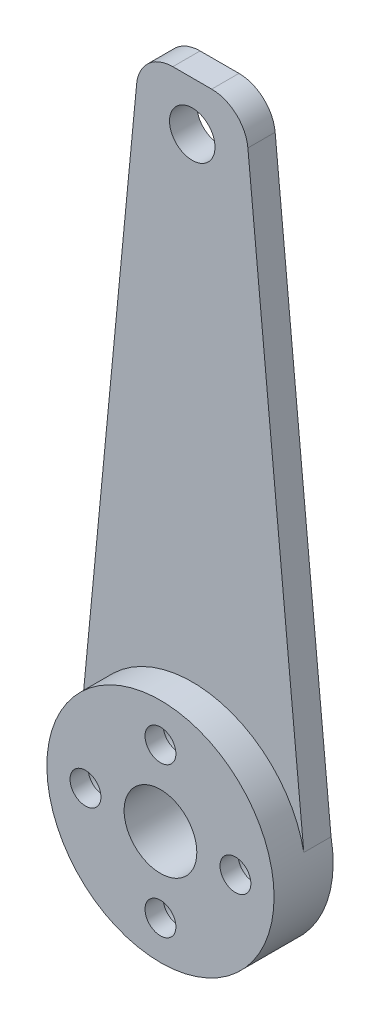
SolidWorks part; units mm, degrees
ref_plane "Plan de face" through (0, 0, 0) normal (0, 0, 1) x (1, 0, 0)
ref_plane "Plan de dessus" through (0, 0, 0) normal (0, 1, 0) x (1, 0, 0)
ref_plane "Plan de droite" through (0, 0, 0) normal (1, 0, 0) x (0, 0, -1)
sketch "Esquisse2" plane through (0, 0, 0) normal (0, 0, 1) x (1, 0, 0)
  circle A0 centre (0, 0) radius 12.5
  circle A1 centre (0, 0) radius 8.25
  dimension "D1" = 25
  dimension "D2" = 16.5
extrude "Boss.-Extru.1" add sketch "Esquisse2" along normal mid plane 6.5 contours A0
sketch "Esquisse3" plane through (0, 0, 0) normal (0, 0, 1) x (1, 0, 0)
  circle A2 centre (0, 8.25) radius 1.2
  circle A3 centre (-8.25, 0) radius 1.2
  circle A4 centre (0, -8.25) radius 1.2
  circle A5 centre (8.25, 0) radius 1.2
  point P3 (-8.25, 0)
  point P11 (0, 8.25)
  point P12 (8.25, 0)
  point P13 (0, -8.25)
  dimension "D1" = 2.4
  dimension "D2" = 2.4
  dimension "D3" = 2.4
  dimension "D4" = 2.4
extrude "Enlèv. mat.-Extru.1" cut sketch "Esquisse3" along normal through all
sketch "Esquisse20" plane through (0, 0, -3.25) normal (0, 0, -1) x (-1, 0, 0)
  line L0 (-12.5, 0) -> (-5.7722, 70.0532)
  line L1 (-5.7722, 70.0532) -> (5.7722, 70.0532)
  line L2 (5.7722, 70.0532) -> (12.5, 0)
  line L3 (12.5, 0) -> (-12.5, 0)
  circle A0 centre (0, 0) radius 12.5 construction
  point P4 (0, 70.0532)
extrude "Boss.-Extru.2" add sketch "Esquisse20" against normal blind 3
sketch "Esquisse10" plane through (0, 0, -3.25) normal (0, 0, -1) x (-1, 0, 0)
  circle A0 centre (-8.25, 0) radius 1.7
  circle A1 centre (0, 8.25) radius 1.7
  circle A2 centre (8.25, 0) radius 1.7
  circle A3 centre (0, -8.25) radius 1.7
  dimension "D1" = 3.4
  dimension "D2" = 3.4
  dimension "D3" = 3.4
  dimension "D4" = 3.4
extrude "Enlèv. mat.-Extru.2" cut sketch "Esquisse10" against normal through all and the other way through all
sketch "Esquisse11" plane through (0, 0, -3.25) normal (0, 0, -1) x (-1, 0, 0)
  line L0 (0, 0) -> (0, -12.5)
  line L1 (0, -12.5) -> (0, 0)
  line L2 (-12.5, 0) -> (0, 0)
  line L3 (0, 0) -> (-8.8388, -8.8388)
  line L4 (-8.8388, -8.8388) -> (8.8388, 8.8388)
  line L5 (-8.8388, -8.8388) -> (-13.3052, -6.8474)
  line L6 (-13.3052, -6.8474) -> (-5.8533, -10.17)
  circle A0 centre (0, 0) radius 12.5 construction
ref_plane "Plan1" through (10.0763, -10.0763, 0) normal (0.7071, -0.7071, 0) x (-0.7071, -0.7071, 0)
sketch "Esquisse13" plane through (10.0763, -10.0763, 0) normal (0.7071, -0.7071, 0) x (-0.7071, -0.7071, 0)
  line L0 (0, 0) -> (0, -3.25)
  line L1 (-12.5, -3.25) -> (12.5, -3.25) construction
  circle A1 centre (0, 0) radius 1
  dimension "D2" = 2
sketch "Esquisse16" plane through (0, 0, 3.25) normal (0, 0, 1) x (1, 0, 0)
  line L0 (0, 0) -> (-6.1179, -5.0018)
sketch "Esquisse17" plane through (0, 0, 3.25) normal (0, 0, 1) x (1, 0, 0)
  circle A0 centre (0, 0) radius 4
  dimension "D1" = 8
extrude "Enlèv. mat.-Extru.8" cut sketch "Esquisse17" against normal through all
sketch "Esquisse14" plane through (0, 0, 0) normal (0, 0, 1) x (1, 0, 0)
  circle A0 centre (0, 0) radius 11.75
  circle A1 centre (0, 0) radius 14.25
  dimension "D1" = 23.5
sketch "Esquisse18" plane through (0, 0, 0) normal (0, 1, 0) x (1, 0, 0)
  line L0 (12.5, 2.5) -> (11.0566, 0)
  line L1 (12.5, -3.25) -> (12.5, 3.25) construction
  line L2 (11.0566, 0) -> (12.5, -2.5)
  line L3 (12.5, -2.5) -> (12.5, 2.5)
  line L4 (-14.25, 0) -> (14.25, 0) construction
  line L5 (11.0566, 0) -> (12.5, 0) construction
  point P4 (12.5, 0)
  point P10 (11.0566, 0)
  dimension "D1" = 30
  dimension "D2" = 30
  dimension "D3" = 5
  dimension "D4" = 1.4434
sketch "Esquisse19" plane through (0, 0, 0) normal (1, 0, 0) x (0, 0, -1)
  line L0 (3.25, 0) -> (-5.3209, 0) construction
ref_plane "Plan2" through (9.7351, -8.3209, 0) normal (-0.6497, -0.7602, 0) x (-0.7602, 0.6497, 0)
fillet "Congé1" radius 4 2 edges at (-5.7722, 70.0532, -1.75) (5.7722, 70.0532, -1.75)
sketch "Esquisse21" plane through (0, 0, -3.25) normal (0, 0, -1) x (-1, 0, 0)
  circle A1 centre (0, 64.6965) radius 2.5
  dimension "D1" = 5
extrude "Enlèv. mat.-Extru.9" cut sketch "Esquisse21" against normal through all
sketch "Sketch1" plane through (0, 0, 3.25) normal (0, 0, 1) x (1, 0, 0)
  circle A0 centre (0, 8.25) radius 2.75
  circle A1 centre (8.25, 0) radius 2.75
  circle A2 centre (-8.25, 0) radius 2.75
  circle A3 centre (0, -8.25) radius 2.75
  dimension "D1" = 5.5
sketch "Sketch2" plane through (0, 0, -3.25) normal (0, 0, -1) x (-1, 0, 0)
  circle A0 centre (0, 8.25) radius 2.75
  circle A1 centre (8.25, 0) radius 2.75
  circle A2 centre (-8.25, 0) radius 2.75
  circle A3 centre (0, -8.25) radius 2.75
  dimension "D1" = 5.5
extrude "Cut-Extrude2" cut sketch "Sketch2" against normal blind 4.5
